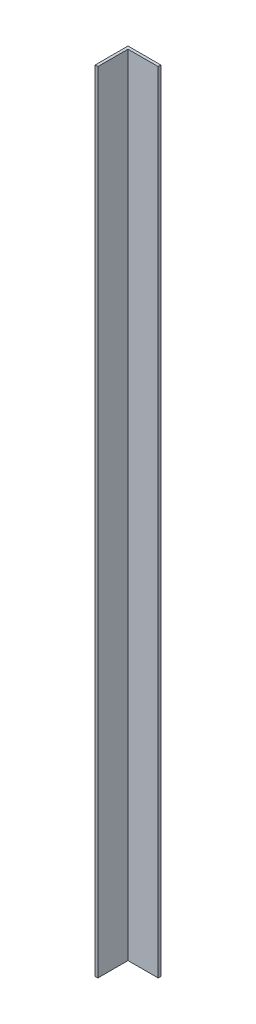
SolidWorks part; units mm, degrees
ref_plane "Front Plane" through (0, 0, 0) normal (0, 0, 1) x (1, 0, 0)
ref_plane "Top Plane" through (0, 0, 0) normal (0, 1, 0) x (1, 0, 0)
ref_plane "Right Plane" through (0, 0, 0) normal (1, 0, 0) x (0, 0, -1)
sketch "Sketch1" plane through (0, 0, 0) normal (0, 1, 0) x (1, 0, 0)
  line L0 (0, 0) -> (0, 19.05)
  line L1 (0, 19.05) -> (19.05, 19.05)
  dimension "D1" = 19.05
  dimension "D2" = 19.05
extrude "Extrude-Thin1" add sketch "Sketch1" along normal blind 457.2 thin
